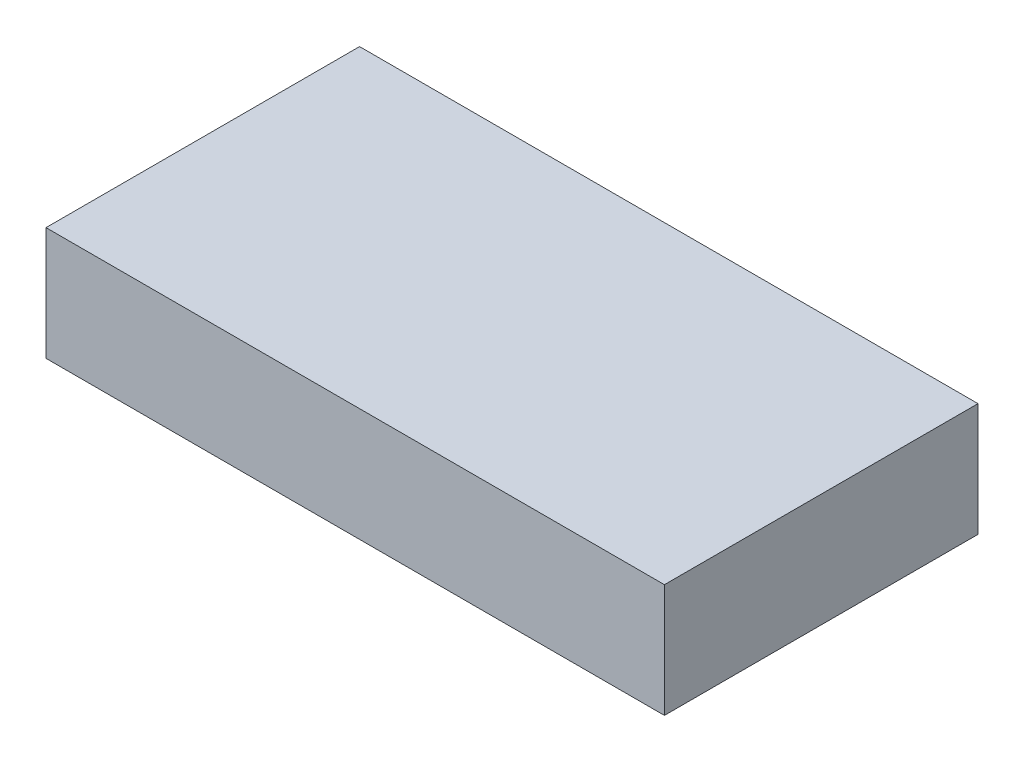
SolidWorks part; units mm, degrees
ref_plane "Front Plane" through (0, 0, 0) normal (0, 0, 1) x (1, 0, 0)
ref_plane "Top Plane" through (0, 0, 0) normal (0, 1, 0) x (1, 0, 0)
ref_plane "Right Plane" through (0, 0, 0) normal (1, 0, 0) x (0, 0, -1)
sketch "Sketch1" plane through (0, 0, 0) normal (0, 1, 0) x (1, 0, 0)
  line L1 (-35.5, 18) -> (35.5, 18)
  line L2 (-35.5, 18) -> (-35.5, -18)
  line L3 (-35.5, -18) -> (35.5, -18)
  line L4 (35.5, 18) -> (35.5, -18)
  line L5 (-35.5, 18) -> (35.5, -18) construction
  line L6 (-35.5, -18) -> (35.5, 18) construction
  point P0 (0, 0)
  dimension "D1" = 71
  dimension "D2" = 36
extrude "Boss-Extrude1" add sketch "Sketch1" along normal mid plane 13
